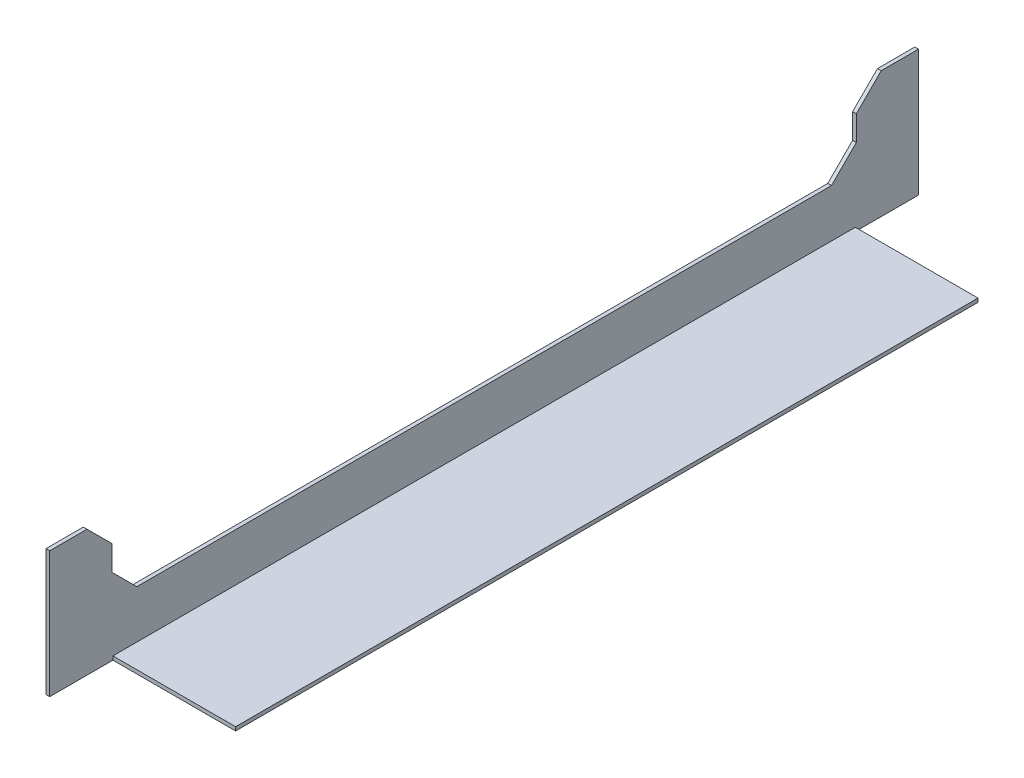
SolidWorks part; units mm, degrees
material "AISI 1015 Acero estirado en frío (SS)"
ref_plane "Alzado" through (0, 0, 0) normal (0, 0, 1) x (1, 0, 0)
ref_plane "Planta" through (0, 0, 0) normal (0, 1, 0) x (1, 0, 0)
ref_plane "Vista lateral" through (0, 0, 0) normal (1, 0, 0) x (0, 0, -1)
sketch "Croquis1" plane through (0, 0, 0) normal (0, 0, 1) x (1, 0, 0)
  line L0 (0, 0) -> (0, 50.8)
  line L1 (0, 0) -> (50.8, 0)
  line L2 (1.5, 1.5) -> (50.8, 1.5)
  line L3 (1.5, 1.5) -> (1.5, 50.8)
  line L4 (1.5, 50.8) -> (0, 50.8)
  line L5 (50.8, 1.5) -> (50.8, 0)
  dimension "D1" = 50.8
  dimension "D2" = 1.5
extrude "Saliente-Extruir1" add sketch "Croquis1" along normal blind 349.2
sketch "Croquis2" plane through (0, 0, 0) normal (-1, 0, 0) x (0, 0, 1)
  line L0 (349.2, 25.4) -> (-34.0342, 25.4) construction
  line L1 (349.2, 50.8) -> (349.2, 0) construction
  line L2 (174.6, 0) -> (174.6, 64.0617) construction
  line L3 (349.2, 0) -> (0, 0) construction
  circle A0 centre (126.6, 25.4) radius 4
  circle A1 centre (222.6, 25.4) radius 4
  circle A2 centre (30.6, 25.4) radius 4
  circle A3 centre (318.6, 25.4) radius 4
  dimension "D1" = 8
  dimension "D2" = 48
  dimension "D3" = 48
  dimension "D4" = 96
  dimension "D5" = 96
extrude "Cortar-Extruir1" cut sketch "Croquis2" against normal blind 2
sketch "Croquis4" plane through (0, 1.5, 0) normal (0, 1, 0) x (1, 0, 0)
  line L0 (1.5, 0) -> (1.5, -25.4)
  line L1 (1.5, -349.2) -> (1.5, 0) construction
  line L2 (1.5, -25.4) -> (50.8, -25.4)
  line L3 (50.8, -349.2) -> (50.8, 0) construction
  line L4 (50.8, -25.4) -> (50.8, 0)
  line L5 (50.8, 0) -> (1.5, 0)
  line L6 (50.8, -174.6) -> (-84.9602, -174.6) construction
  line L7 (1.5, -349.2) -> (1.5, -323.8)
  line L8 (50.8, -349.2) -> (1.5, -349.2)
  line L9 (50.8, -323.8) -> (50.8, -349.2)
  line L10 (1.5, -323.8) -> (50.8, -323.8)
  dimension "D1" = 25.4
  dimension "D2" = 49.3
extrude "Cortar-Extruir2" cut sketch "Croquis4" against normal blind 2
sketch "Croquis5" plane through (0, 0, 0) normal (-1, 0, 0) x (0, 0, 1)
  line L0 (324.2, 0) -> (324.2, 50.8) construction
  line L1 (349.2, 0) -> (0, 0) construction
  line L2 (349.2, 50.8) -> (0, 50.8) construction
  line L3 (349.2, 50.8) -> (349.2, 0) construction
  line L4 (174.6, 0) -> (174.6, 50.8) construction
  line L5 (349.2, 20.8) -> (0, 20.8) construction
  line L6 (0, 50.8) -> (0, 0) construction
  line L7 (324.2, 50.8) -> (324.2, 20.8)
  line L8 (324.2, 20.8) -> (25, 20.8)
  line L9 (25, 50.8) -> (25, 20.8)
  line L10 (324.2, 50.8) -> (25, 50.8)
  point P17 (174.6, 20.8)
  dimension "D1" = 25
  dimension "D2" = 30
extrude "Cortar-Extruir3" cut sketch "Croquis5" against normal blind 2
chamfer "Chaflán1" distance 10 angle 45 4 edges at (0.75, 50.8, 25) (0.75, 20.8, 25) (0.75, 50.8, 324.2) (0.75, 20.8, 324.2)
